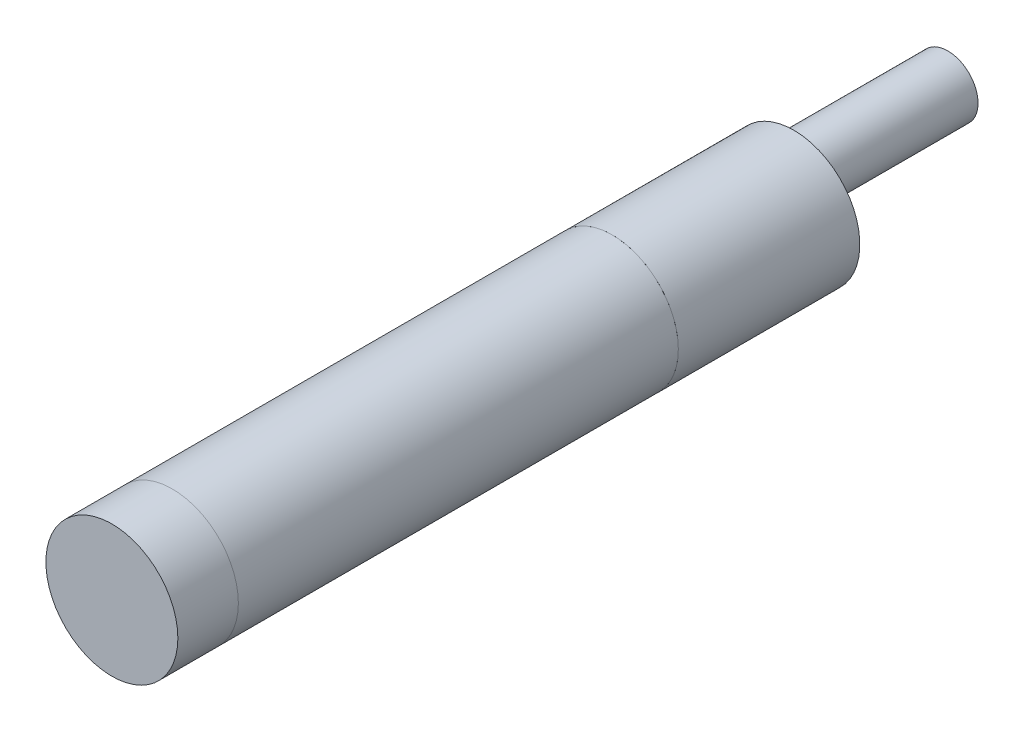
SolidWorks part; units mm, degrees
ref_plane "Front" through (0, 0, 0) normal (0, 0, 1) x (1, 0, 0)
ref_plane "Top" through (0, 0, 0) normal (0, 1, 0) x (1, 0, 0)
ref_plane "Right" through (0, 0, 0) normal (1, 0, 0) x (0, 0, -1)
sketch "Sketch1" plane through (0, 0, 0) normal (0, 0, 1) x (1, 0, 0)
  circle A0 centre (0, 0) radius 6
  dimension "D1" = 12
extrude "Boss-Extrude1" add sketch "Sketch1" along normal blind 40
sketch "Sketch2" plane through (0, 0, 40) normal (0, 0, 1) x (1, 0, 0)
  circle A0 centre (0, 0) radius 6
extrude "Boss-Extrude2" add sketch "Sketch2" along normal blind 5.5 separate body
sketch "Sketch3" plane through (0, 0, 0) normal (0, 0, -1) x (-1, 0, 0)
  circle A0 centre (0, 0) radius 6
extrude "Boss-Extrude3" add sketch "Sketch3" along normal blind 16.5 separate body
sketch "Sketch4" plane through (0, 0, -16.5) normal (0, 0, -1) x (-1, 0, 0)
  line L0 (0, 0) -> (0, 6) construction
  circle A0 centre (0, 0) radius 6 construction
  circle A1 centre (0, 2.4933) radius 2.75
  dimension "D1" = 5.5
extrude "Boss-Extrude4" add sketch "Sketch4" along normal blind 14
